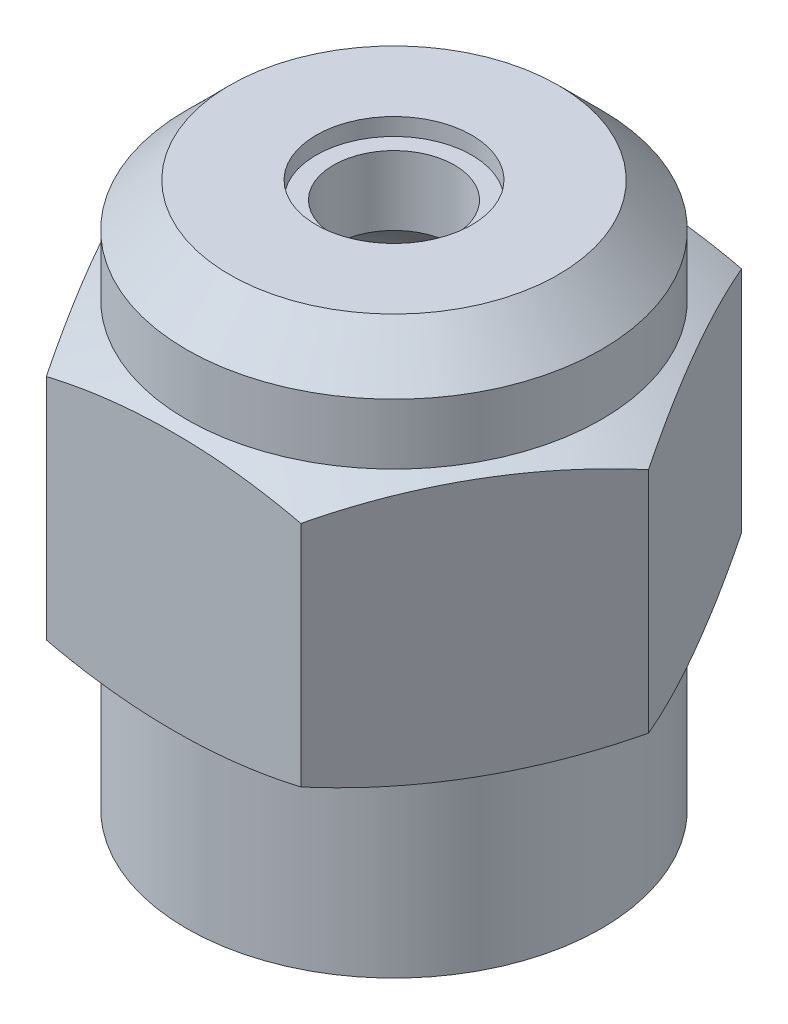
SolidWorks part; units mm, degrees
ref_plane "FRONT" through (0, 0, 0) normal (0, 0, 1) x (1, 0, 0)
ref_plane "TOP" through (0, 0, 0) normal (0, 1, 0) x (1, 0, 0)
ref_plane "SIDE" through (0, 0, 0) normal (1, 0, 0) x (0, 0, -1)
sketch "Sketch1" plane through (0, 0, 0) normal (0, 0, 1) x (1, 0, 0)
  line L0 (0, 0) -> (0, 16.002) construction
  line L1 (6.096, 0) -> (6.096, 14.732)
  line L2 (6.096, 14.732) -> (4.826, 16.002)
  line L3 (4.826, 16.002) -> (2.286, 16.002)
  line L4 (1.778, 15.494) -> (1.778, 13.462)
  line L5 (6.096, 0) -> (4.191, 0)
  line L6 (4.191, 0) -> (4.191, 9.6668)
  line L7 (1.778, 15.494) -> (2.286, 15.494)
  line L8 (2.286, 15.494) -> (2.286, 16.002)
  arc A0 (4.191, 9.6668) -> (1.778, 13.462) centre (0, 9.6668) ccw
  dimension "D1" = 6.096
  dimension "D2" = 4.191
  dimension "D3" = 1.27
  dimension "D4" = 1.27
  dimension "D5" = 1.778
  dimension "D6" = 2.54
  dimension "D7" = 16.002
  dimension "D8" = 0.508
  dimension "D9" = 2.286
revolve "Base-Revolve" add sketch "Sketch1" angle 360 about L0
ref_plane "Plane4" through (0, 12.954, 0) normal (0, 1, 0) x (-1, 0, 0)
sketch "Sketch3" plane through (0, 12.954, 0) normal (0, 1, 0) x (-1, 0, 0)
  line L0 (3.7395, -6.477) -> (-3.7395, -6.477)
  line L1 (-3.7395, -6.477) -> (-7.479, 0)
  line L2 (-7.479, 0) -> (-3.7395, 6.477)
  line L3 (-3.7395, 6.477) -> (3.7395, 6.477)
  line L4 (3.7395, 6.477) -> (7.479, 0)
  line L5 (7.479, 0) -> (3.7395, -6.477)
  circle A0 centre (0, 0) radius 6.477 construction
  circle A2 centre (0, 0) radius 6.096 construction
  circle A3 centre (0, 0) radius 6.096
  dimension "D1" = 12.954
extrude "Boss-Extrude1" add sketch "Sketch3" against normal blind 7.874
ref_plane "Plane5" through (0, 9.017, 0) normal (0, 1, 0) x (-1, 0, 0)
sketch "Sketch4" plane through (0, 0, 0) normal (0, 0, 1) x (1, 0, 0)
  line L0 (0, 0) -> (0, 16.002) construction
  line L3 (4.826, 16.002) -> (-4.826, 16.002) construction
  line L4 (4.826, 12.954) -> (-4.826, 12.954) construction
  line L5 (7.479, 5.08) -> (7.479, 12.954) construction
  line L6 (6.096, 12.954) -> (6.096, 14.732) construction
  line L7 (7.479, 12.954) -> (3.7395, 12.954) construction
  line L10 (7.479, 12.954) -> (6.096, 12.954)
  line L11 (7.479, 12.3698) -> (7.479, 12.954)
  line L12 (0, 0) -> (0, 16.002) construction
  arc A0 (6.096, 12.954) -> (7.479, 12.3698) centre (0, -3.4064) cw
  dimension "D1" = 0.5842
revolve "Cut-Revolve1" cut sketch "Sketch4" angle 360 about L12
mirror "Mirror1" about plane through (0, 9.017, 0) normal (0, 1, 0) of "Cut-Revolve1"
